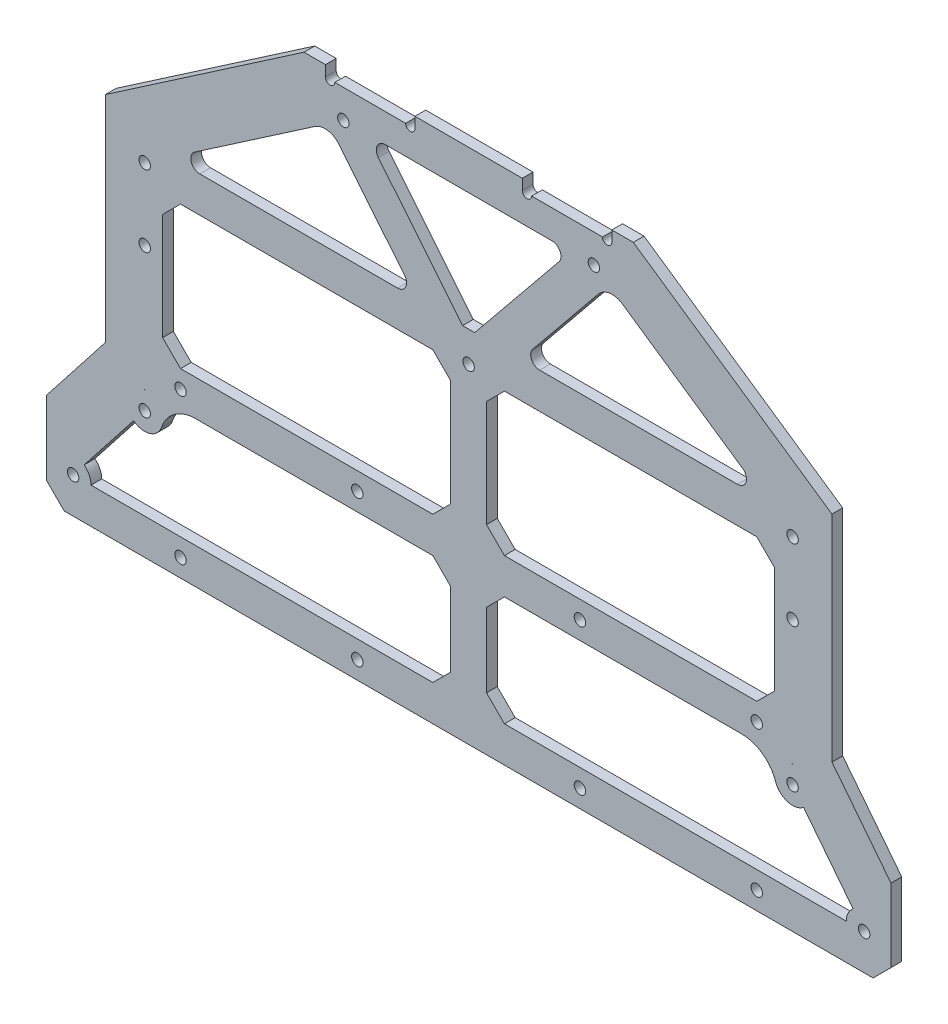
SolidWorks part; units mm, degrees
material "Thornel Mat VMA"
ref_plane "前视基准面" through (0, 0, 0) normal (0, 0, 1) x (1, 0, 0)
ref_plane "上视基准面" through (0, 0, 0) normal (0, 1, 0) x (1, 0, 0)
ref_plane "右视基准面" through (0, 0, 0) normal (1, 0, 0) x (0, 0, -1)
sketch "草图1" plane through (0, 0, 0) normal (0, 0, 1) x (1, 0, 0)
  line L0 (0, 0) -> (0, -98) construction
  line L1 (-35, 0) -> (35, 0) construction
  line L2 (-35, 0) -> (-35, -38) construction
  line L3 (-35, -38) -> (-90.5, -38) construction
  line L4 (-90.5, -38) -> (-90.5, -98) construction
  line L5 (-90.5, -98) -> (-110.5, -98) construction
  line L6 (-110.5, -98) -> (-110.5, -123.5) construction
  line L7 (35, 0) -> (35, -38) construction
  line L8 (35, -38) -> (90.5, -38) construction
  line L9 (90.5, -38) -> (90.5, -98) construction
  line L10 (90.5, -98) -> (110.5, -98) construction
  line L11 (110.5, -98) -> (110.5, -123.5) construction
  line L12 (-90.5, -98) -> (90.5, -98) construction
  line L13 (-121.5, -87) -> (-121.5, -123.5)
  line L14 (-101.5, -87) -> (-121.5, -87)
  line L15 (-101.5, -27) -> (-101.5, -87)
  line L16 (-46, -27) -> (-101.5, -27)
  line L17 (-46, 11) -> (-46, -27)
  line L18 (-46, 11) -> (46, 11)
  line L19 (46, 11) -> (46, -27)
  line L20 (46, -27) -> (101.5, -27)
  line L21 (101.5, -27) -> (101.5, -87)
  line L22 (101.5, -87) -> (121.5, -87)
  line L23 (121.5, -87) -> (121.5, -123.5)
  line L24 (-121.5, -123.5) -> (-121.5, -133.5)
  line L25 (-121.5, -133.5) -> (121.5, -133.5)
  line L26 (121.5, -133.5) -> (121.5, -123.5)
  circle A0 centre (-110.5, -123.5) radius 1.6
  circle A1 centre (-90.5, -98) radius 1.6
  circle A2 centre (-90.5, -38) radius 1.6
  circle A3 centre (-35, 0) radius 1.6
  circle A4 centre (110.5, -123.5) radius 1.6
  circle A5 centre (90.5, -98) radius 1.6
  circle A6 centre (90.5, -38) radius 1.6
  circle A7 centre (35, 0) radius 1.6
  dimension "D7" = 3.2
  dimension "D8" = 3.2
  dimension "D9" = 3.2
  dimension "D10" = 3.2
  dimension "D1" = 70
  dimension "D2" = 38
  dimension "D3" = 55.5
  dimension "D4" = 60
  dimension "D5" = 20
  dimension "D6" = 25.5
  dimension "D12" = 10
  dimension "D11" = 11
extrude "凸台-拉伸1" add sketch "草图1" along normal blind 3
sketch "草图4" plane through (0, 0, 0) normal (0, 0, -1) x (-1, 0, 0)
  line L0 (-101.5, -27) -> (-46, 11)
  line L1 (-46, 11) -> (-46, -27)
  line L2 (-46, -27) -> (-101.5, -27)
  line L3 (46, 11) -> (101.5, -27)
  line L4 (101.5, -27) -> (46, -27)
  line L5 (46, -27) -> (46, 11)
extrude "凸台-拉伸2" add sketch "草图4" against normal up to surface (3 mm away) up to face at (88.9, -38, 3)
sketch "草图5" plane through (0, 0, 3) normal (0, 0, 1) x (1, 0, 0)
  line L0 (0, 11) -> (0, -79.3684) construction
  line L1 (46, 11) -> (-46, 11) construction
  line L2 (-86.3744, -35.1752) -> (-39.1256, -2.8248)
  line L3 (-90.5, -43) -> (-90.5, -93)
  line L4 (-93.5857, -101.9343) -> (-107.4143, -119.5657)
  line L5 (-105.5, -123.5) -> (105.5, -123.5)
  line L6 (107.4143, -119.5657) -> (93.5857, -101.9343)
  line L7 (90.5, -93) -> (90.5, -43)
  line L8 (86.3744, -35.1752) -> (39.1256, -2.8248)
  line L9 (30, 0) -> (-30, 0)
  arc A0 (-39.1256, -2.8248) -> (-30, 0) centre (-35, 0) ccw
  arc A1 (30, 0) -> (39.1256, -2.8248) centre (35, 0) ccw
  arc A2 (-90.5, -43) -> (-86.3744, -35.1752) centre (-90.5, -38) ccw
  arc A3 (-93.5857, -101.9343) -> (-90.5, -93) centre (-90.5, -98) ccw
  arc A4 (-105.5, -123.5) -> (-107.4143, -119.5657) centre (-110.5, -123.5) ccw
  arc A5 (105.5, -123.5) -> (107.4143, -119.5657) centre (110.5, -123.5) cw
  arc A6 (93.5857, -101.9343) -> (90.5, -93) centre (90.5, -98) cw
  arc A7 (90.5, -43) -> (86.3744, -35.1752) centre (90.5, -38) cw
  dimension "D1" = 10
  dimension "D3" = 10
  dimension "D4" = 10
  dimension "D5" = 10
extrude "切除-拉伸2" cut sketch "草图5" against normal up to next
sketch "草图6" plane through (-121.5, 0, 0) normal (-1, 0, 0) x (0, 0, 1)
  line L4 (0, -87) -> (0, -133.5)
  line L5 (0, -133.5) -> (3, -133.5)
  line L6 (3, -133.5) -> (3, -87)
  line L7 (3, -87) -> (0, -87)
  line L8 (0, -87) -> (0, -133.5)
  line L9 (0, -133.5) -> (3, -133.5)
  line L10 (3, -133.5) -> (3, -87)
  line L11 (3, -87) -> (0, -87)
  dimension "D1" = 0
extrude "切除-拉伸3" cut sketch "草图6" against normal blind 3.5
sketch "草图7" plane through (121.5, 0, 0) normal (1, 0, 0) x (0, 0, -1)
  line L4 (0, -133.5) -> (0, -87)
  line L5 (0, -87) -> (-3, -87)
  line L6 (-3, -87) -> (-3, -133.5)
  line L7 (-3, -133.5) -> (0, -133.5)
  line L8 (0, -133.5) -> (0, -87)
  line L9 (0, -87) -> (-3, -87)
  line L10 (-3, -87) -> (-3, -133.5)
  line L11 (-3, -133.5) -> (0, -133.5)
  dimension "D1" = 0
extrude "切除-拉伸4" cut sketch "草图7" against normal blind 3.5
sketch "草图8" plane through (0, 0, 3) normal (0, 0, 1) x (1, 0, 0)
  line L0 (-101.5, -87) -> (-118, -108.0375)
  line L1 (-118, -133.5) -> (-118, -87) construction
  line L2 (-93.5857, -101.9343) -> (-107.4143, -119.5657) construction
  line L3 (-118, -108.0375) -> (-118, -87)
  line L4 (-118, -87) -> (-101.5, -87)
extrude "切除-拉伸5" cut sketch "草图8" against normal up to next
sketch "草图9" plane through (0, 0, 3) normal (0, 0, 1) x (1, 0, 0)
  line L0 (101.5, -87) -> (118, -108.0375)
  line L1 (118, -87) -> (118, -133.5) construction
  line L4 (107.4143, -119.5657) -> (93.5857, -101.9343) construction
  line L5 (101.5, -87) -> (118, -87)
  line L6 (118, -87) -> (118, -108.0375)
extrude "切除-拉伸6" cut sketch "草图9" against normal up to next
sketch "草图11" plane through (0, 0, 3) normal (0, 0, 1) x (1, 0, 0)
  line L0 (-90.5, -38) -> (90.5, -38)
extrude "拉伸-薄壁2" add sketch "草图11" against normal up to surface (3 mm away) thin up to face at (0, -65.6941, 0) thin type mid plane wall 10
sketch "草图12" plane through (0, 0, 0) normal (0, 0, -1) x (-1, 0, 0)
  line L0 (-90.5, -39.6) -> (-90.5, -36.4) construction
  line L1 (90.5, -36.4) -> (90.5, -39.6) construction
  circle A0 centre (-90.5, -38) radius 1.6
  circle A1 centre (90.5, -38) radius 1.6
extrude "切除-拉伸7" cut sketch "草图12" against normal up to next
sketch "草图13" plane through (0, 0, 0) normal (0, 0, -1) x (-1, 0, 0)
  line L0 (-35, 0) -> (0, -43)
  line L1 (-90.5, -43) -> (90.5, -43) construction
  line L2 (0, -43) -> (35, 0)
extrude "拉伸-薄壁4" add sketch "草图13" against normal up to surface (3 mm away) thin up to face at (-88.9, -38, 3) thin type mid plane wall 10
sketch "草图14" plane through (0, 0, 3) normal (0, 0, 1) x (1, 0, 0)
  line L0 (0, -50.9205) -> (6.4469, -43)
  line L1 (6.4469, -43) -> (-6.4469, -43)
  line L2 (-6.4469, -43) -> (0, -50.9205)
extrude "切除-拉伸8" cut sketch "草图14" against normal up to next
sketch "草图15" plane through (0, 0, 3) normal (0, 0, 1) x (1, 0, 0)
  line L0 (0, -33) -> (0, -133.5)
  line L3 (-1.6926, -33) -> (1.6926, -33) construction
  line L4 (-118, -133.5) -> (118, -133.5) construction
extrude "拉伸-薄壁5" add sketch "草图15" against normal up to surface (3 mm away) thin up to face at (0, -96.5889, 0) thin type mid plane wall 10
sketch "草图16" plane through (0, 0, 0) normal (0, 0, -1) x (-1, 0, 0)
  line L0 (105.5, -123.5) -> (105.5, -133.5) construction
  line L1 (118, -133.5) -> (-118, -133.5) construction
  line L2 (105.5, -128.5) -> (80.5, -128.5) construction
  line L3 (80.5, -128.5) -> (31.1, -128.5) construction
  line L4 (0, -133.5) -> (0, -100.3714) construction
  circle A0 centre (80.5, -128.5) radius 1.6
  circle A1 centre (31.1, -128.5) radius 1.6
  circle A2 centre (-80.5, -128.5) radius 1.6
  circle A3 centre (-31.1, -128.5) radius 1.6
  dimension "D2" = 3.2
  dimension "D4" = 3.2
  dimension "D1" = 25
  dimension "D3" = 49.4
extrude "切除-拉伸9" cut sketch "草图16" against normal up to next
sketch "草图17" plane through (0, 0, 0) normal (0, 0, -1) x (-1, 0, 0)
  line L0 (80.5, -128.5) -> (80.5, -87.8) construction
  line L1 (90.5, -87.8) -> (-90.5, -87.8)
  line L2 (90.5, -93) -> (90.5, -43) construction
  line L3 (-90.5, -43) -> (-90.5, -93) construction
  dimension "D1" = 40.7
extrude "拉伸-薄壁6" add sketch "草图17" against normal up to surface (3 mm away) thin up to face at (32.7, -128.5, 3) thin type mid plane wall 10
sketch "草图18" plane through (0, 0, 0) normal (0, 0, -1) x (-1, 0, 0)
  line L0 (31.1, -128.5) -> (31.1, -87.8) construction
  line L1 (80.5, -128.5) -> (80.5, -87.8) construction
  line L2 (0, -133.5) -> (0, -84.2485) construction
  line L3 (118, -133.5) -> (-118, -133.5) construction
  circle A0 centre (31.1, -87.8) radius 1.6
  circle A1 centre (80.5, -87.8) radius 1.6
  circle A2 centre (-80.5, -87.8) radius 1.6
  circle A3 centre (-31.1, -87.8) radius 1.6
  dimension "D2" = 3.2
  dimension "D3" = 3.2
  dimension "D1" = 40.7
extrude "切除-拉伸10" cut sketch "草图18" against normal up to next
sketch "草图19" plane through (0, 0, 0) normal (0, 0, -1) x (-1, 0, 0)
  line L0 (-36.2409, -1.01) -> (-33.7591, 1.01) construction
  line L1 (33.7591, 1.01) -> (36.2409, -1.01) construction
  circle A0 centre (-35, 0) radius 1.6
  circle A1 centre (35, 0) radius 1.6
  dimension "D1" = 3.2
extrude "切除-拉伸11" cut sketch "草图19" against normal up to next
sketch "草图20" plane through (0, 0, 0) normal (0, 0, -1) x (-1, 0, 0)
  line L0 (-85.7739, -99.6323) -> (-83.4142, -92.8)
  line L1 (-5, -92.8) -> (-90.5, -92.8) construction
  line L2 (-83.4142, -92.8) -> (-90.5, -92.8)
  line L3 (-90.5, -92.8) -> (-85.7739, -99.6323)
  line L4 (0, -133.5) -> (0, -102.5301) construction
  line L5 (118, -133.5) -> (-118, -133.5) construction
  line L6 (90.5, -92.8) -> (85.7739, -99.6323)
  line L7 (83.4142, -92.8) -> (90.5, -92.8)
  line L8 (85.7739, -99.6323) -> (83.4142, -92.8)
  arc A0 (-93.5857, -101.9343) -> (-90.5, -93) centre (-90.5, -98) ccw construction
extrude "凸台-拉伸3" add sketch "草图20" against normal up to surface (3 mm away) up to face at (-33.4, 0, 3)
fillet "圆角1" radius 10 2 edges at (83.4142, -92.8, 1.5) (-83.4142, -92.8, 1.5)
chamfer "倒角1" distance 5 angle 45 2 edges at (118, -133.5, 1.5) (-118, -133.5, 1.5)
chamfer "倒角2" distance 5 angle 45 12 edges at (5, -123.5, 1.5) (-5, -123.5, 1.5) (5, -43, 1.5) (-5, -43, 1.5) (5, -82.8, 1.5) (5, -92.8, 1.5) (-5, -82.8, 1.5) (-5, -92.8, 1.5) (-90.5, -43, 1.5) (-90.5, -82.8, 1.5) (90.5, -82.8, 1.5) (90.5, -43, 1.5)
sketch "草图21" plane through (0, 0, 0) normal (0, 0, -1) x (-1, 0, 0)
  line L0 (0, 11) -> (0, 8) construction
  line L1 (-46, 11) -> (46, 11) construction
  line L2 (15, 8) -> (-15, 8) construction
  line L3 (-15, 8) -> (-15, 11)
  line L4 (-15, 11) -> (-40, 11)
  line L5 (-40, 11) -> (-40, 8)
  line L6 (-37.4, 8) -> (-17.6, 8)
  line L7 (37.4, 8) -> (17.6, 8)
  line L8 (40, 11) -> (40, 8)
  line L9 (15, 11) -> (40, 11)
  line L10 (15, 8) -> (15, 11)
  arc A0 (-40, 8) -> (-37.4, 8) centre (-38.7, 8) ccw
  arc A1 (-17.6, 8) -> (-15, 8) centre (-16.3, 8) ccw
  arc A2 (17.6, 8) -> (15, 8) centre (16.3, 8) cw
  arc A3 (40, 8) -> (37.4, 8) centre (38.7, 8) cw
  dimension "D4" = 2.6
  dimension "D5" = 2.6
  dimension "D1" = 3
  dimension "D2" = 15
  dimension "D3" = 25
extrude "切除-拉伸12" cut sketch "草图21" against normal up to next
sketch "草图22" plane through (0, 0, 0) normal (0, 0, -1) x (-1, 0, 0)
  line L0 (0, -33) -> (0, -41.5) construction
  line L1 (-1.6926, -33) -> (1.6926, -33) construction
  circle A0 centre (0, -41.5) radius 1.6
  dimension "D2" = 3.2
  dimension "D1" = 8.5
extrude "切除-拉伸13" cut sketch "草图22" against normal up to next
fillet "圆角2" radius 5 2 edges at (-39.1256, -2.8248, 1.5) (39.1256, -2.8248, 1.5)
fillet "圆角3" radius 2.5 6 edges at (-83.1974, -33, 1.5) (83.1974, -33, 1.5) (-14.5865, -33, 1.5) (14.5865, -33, 1.5) (-28.5531, 0, 1.5) (28.5531, 0, 1.5)
sketch "草图23" plane through (0, 0, 0) normal (0, 0, -1) x (-1, 0, 0)
  line L0 (-85.5, -43) -> (-85.5, -82.8)
  line L1 (-90.5, -48) -> (-85.5, -43) construction
  line L2 (-90.5, -48) -> (-90.5, -77.8) construction
  line L3 (-85.5, -82.8) -> (-90.5, -77.8) construction
  line L4 (-90.5, -48) -> (-85.5, -43)
  line L5 (-90.5, -48) -> (-90.5, -77.8)
  line L6 (-85.5, -82.8) -> (-90.5, -77.8)
  line L7 (85.5, -82.8) -> (85.5, -43)
  line L8 (85.5, -43) -> (90.5, -48) construction
  line L9 (90.5, -77.8) -> (90.5, -48) construction
  line L10 (90.5, -77.8) -> (85.5, -82.8) construction
  line L11 (85.5, -43) -> (90.5, -48)
  line L12 (90.5, -77.8) -> (90.5, -48)
  line L13 (90.5, -77.8) -> (85.5, -82.8)
extrude "凸台-拉伸4" add sketch "草图23" against normal up to surface (3 mm away) up to face at (1.6, -41.5, 3)
sketch "草图24" plane through (0, 0, 0) normal (0, 0, -1) x (-1, 0, 0)
  line L0 (-90.5, -38) -> (-90.5, -58) construction
  line L1 (0, -133.5) -> (0, -58) construction
  line L2 (113, -133.5) -> (-113, -133.5) construction
  circle A0 centre (-90.5, -58) radius 1.6
  circle A1 centre (90.5, -58) radius 1.6
  dimension "D2" = 3.2
  dimension "D1" = 20
extrude "切除-拉伸14" cut sketch "草图24" against normal up to next
chamfer "倒角3" distance 5 angle 45 4 edges at (-85.5, -43, 1.5) (-85.5, -82.8, 1.5) (85.5, -82.8, 1.5) (85.5, -43, 1.5)
